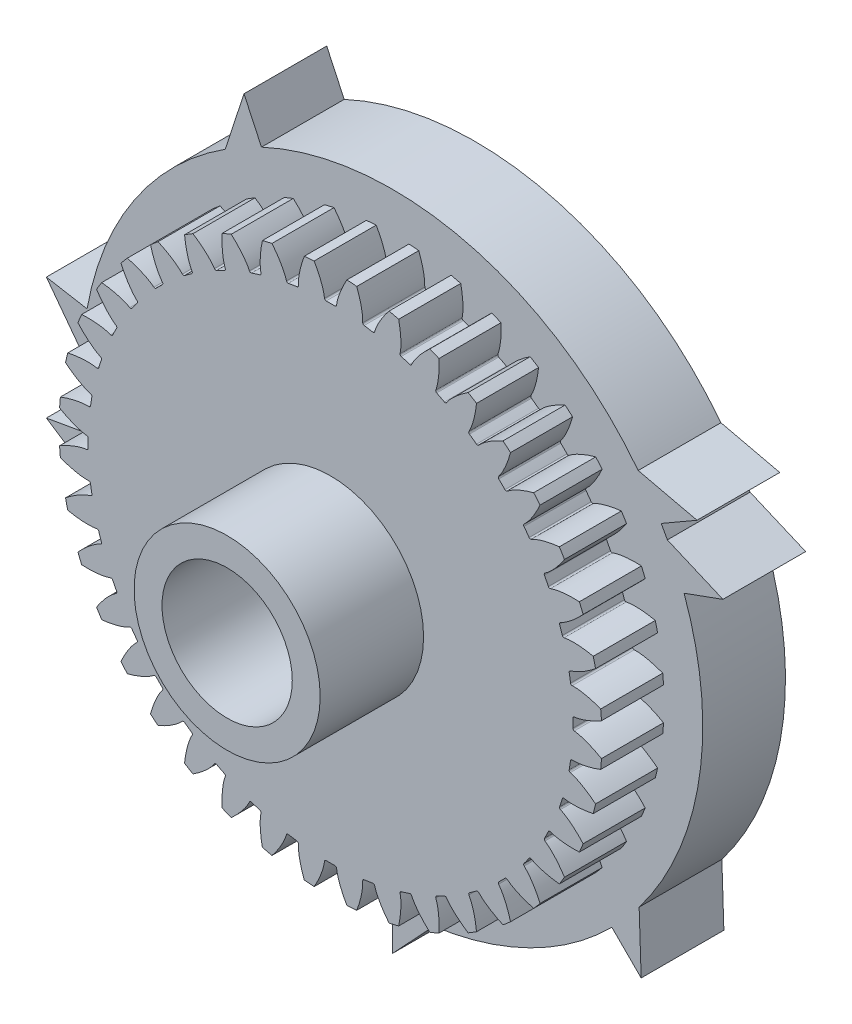
SolidWorks part; units mm, degrees
ref_plane "Front Plane" through (0, 0, 0) normal (0, 0, 1) x (1, 0, 0)
ref_plane "Top Plane" through (0, 0, 0) normal (0, 1, 0) x (1, 0, 0)
ref_plane "Right Plane" through (0, 0, 0) normal (1, 0, 0) x (0, 0, -1)
sketch "D" plane through (0, 0, 0) normal (0, 0, 1) x (1, 0, 0)
  circle A0 centre (0, 0) radius 12.5 construction
  dimension "D1" = 25
sketch "De, Di, Db" plane through (0, 0, 0) normal (0, 0, 1) x (1, 0, 0)
  circle A0 centre (0, 0) radius 11.7462 construction
  circle A1 centre (0, 0) radius 13.125 construction
  circle A2 centre (0, 0) radius 11.7188 construction
  point P7 (0, 0)
  dimension "D1" = 23.4923
  dimension "D2" = 26.25
  dimension "D3" = 23.4375
sketch "Sketch4" plane through (0, 0, 0) normal (0, 0, 1) x (1, 0, 0)
  circle A0 centre (0, 0) radius 13.125 construction
  circle A1 centre (0, 0) radius 13.125
extrude "Addendum Extruded" add sketch "Sketch4" along normal mid plane 3
sketch "Tooth Profile Curve" plane through (0, 0, 0) normal (0, 0, 1) x (1, 0, 0)
  line L0 (0, 0) -> (13.125, 0) construction
  line L1 (0, 0) -> (11.7427, 0.287) construction
  line L2 (0, 0) -> (12.4904, 0.4907) construction
  line L3 (11.7427, 0.287) -> (11.7153, 0.2863)
  line L4 (11.7188, 0) -> (13.125, 0)
  circle A0 centre (0, 0) radius 11.7462 construction
  circle A1 centre (0, 0) radius 13.125 construction
  circle A2 centre (0, 0) radius 11.7188 construction
  circle A3 centre (0, 0) radius 12.5 construction
  arc A4 (11.7153, 0.2863) -> (11.7188, 0) centre (0, 0) cw
  arc A5 (13.125, 0) -> (13.1011, 0.7919) centre (0, 0) ccw
  spline S0 degree 4 poles (11.7427, 0.287) (11.7513, 0.2874) (11.7756, 0.289) (11.8214, 0.2944) (11.8958, 0.3063) (11.9898, 0.3261) (12.1104, 0.3571) (12.2508, 0.4002) (12.4033, 0.4546) (12.567, 0.5213) (12.728, 0.5943) (12.8863, 0.6731) (13.0419, 0.757) (13.2276, 0.8647) (13.4463, 1.0026) (13.6956, 1.1758) (13.9706, 1.3865) (14.2417, 1.6158) (14.5008, 1.8533) (14.7531, 2.1063) (14.9904, 2.3604) (15.2265, 2.6369) (15.4391, 2.8987) (15.6651, 3.2052) (15.844, 3.4566) (16.0663, 3.8016) (16.1935, 4.0093) (16.3375, 4.2568) (16.3989, 4.369) (16.4368, 4.438) knots 0 0 0 0 0 0.005377 0.015084 0.028532 0.04661 0.064855 0.092111 0.119476 0.146842 0.174209 0.201575 0.228941 0.256307 0.307035 0.361767 0.4165 0.471232 0.525964 0.580697 0.635429 0.690161 0.744894 0.799626 0.854358 0.909091 0.954545 1 1 1 1 1 construction
  spline S1 degree 4 poles (11.7427, 0.287) (11.7513, 0.2874) (11.7756, 0.289) (11.8214, 0.2944) (11.8958, 0.3063) (11.9898, 0.3261) (12.1104, 0.3571) (12.2508, 0.4002) (12.4033, 0.4546) (12.567, 0.5213) (12.728, 0.5943) (12.8863, 0.6731) (13.0419, 0.757) (13.2276, 0.8647) (13.4463, 1.0026) (13.6956, 1.1758) (13.9706, 1.3865) (14.2417, 1.6158) (14.5008, 1.8533) (14.7531, 2.1063) (14.9904, 2.3604) (15.2265, 2.6369) (15.4391, 2.8987) (15.6651, 3.2052) (15.844, 3.4566) (16.0181, 3.7268) (16.1013, 3.8598) (16.1431, 3.9284) knots 0 0 0 0 0 0.005377 0.015084 0.028532 0.04661 0.064855 0.092111 0.119476 0.146842 0.174209 0.201575 0.228941 0.256307 0.307035 0.361767 0.4165 0.471232 0.525964 0.580697 0.635429 0.690161 0.744894 0.799626 0.854358 0.909091 0.909091 0.909091 0.909091 0.909091
  dimension "D1" = 2.25
  dimension "D2" = 0.85
  dimension "D3" = 1.4
extrude "1/2 Tooth Cut" cut sketch "Tooth Profile Curve" against normal mid plane 4
ref_plane "Plane of Mirroring" through (0, 0, 0) normal (0, 1, 0) x (1, 0, 0)
mirror "Mirror Tooth Cut" about plane through (0, 0, 0) normal (0, 1, 0) of "1/2 Tooth Cut"
fillet "Roots Fillet" radius 0.0781 3 edges at (11.7427, -0.287, 0) (11.7153, -0.2863, 0) (11.7153, 0.2863, 0)
pattern_circular "Circular Pattern of Teeth" count 40 over 360 about axis through (0, 0, -2) along (0, 0, 1) of "Mirror Tooth Cut", "1/2 Tooth Cut", "Roots Fillet"
sketch "Sketch5" plane through (0, 0, 0) normal (0, 0, 1) x (1, 0, 0)
  line L0 (1, 4) -> (-1, 4) construction
  line L1 (-1, 5) -> (1, 5)
  line L2 (-1, 5) -> (-1, 3.873)
  line L5 (1, 4) -> (1, 5)
  line L6 (1, 4) -> (1, 3.873)
  arc A0 (-1, 3.873) -> (1, 3.873) centre (0, 0) ccw
  circle A1 centre (0, 0) radius 4 construction
  point P9 (0, 5)
  dimension "D1" = 8
  dimension "D2" = 1
  dimension "D3" = 2
extrude "Bore and Keyway" cut sketch "Sketch5" against normal through all both and the other way through all
sketch "Sketch6" [suppressed] plane through (0, 0, 0) normal (0, 0, 1) x (1, 0, 0)
  line L6 (41.8591, 5.9947) -> (34.5048, 4.9415) construction
  line L7 (37.3883, 19.7543) -> (30.8195, 16.2837) construction
  line L8 (41.8591, 5.9947) -> (34.5048, 4.9415)
  line L9 (37.3883, 19.7543) -> (30.8195, 16.2837)
  arc A14 (52.1159, 14.1398) -> (50.4738, 19.1936) centre (0, 0) ccw construction
  arc A20 (34.5048, 4.9415) -> (33.5461, 3.7044) centre (34.6643, 3.8278) ccw construction
  arc A29 (29.3167, 16.721) -> (30.8195, 16.2837) centre (30.294, 17.2784) ccw construction
  circle A30 centre (0, 0) radius 33.75 construction
  arc A31 (52.1159, 14.1398) -> (50.4738, 19.1936) centre (0, 0) ccw
  arc A32 (34.5048, 4.9415) -> (33.5461, 3.7044) centre (34.6643, 3.8278) ccw
  arc A33 (29.3167, 16.721) -> (30.8195, 16.2837) centre (30.294, 17.2784) ccw
  arc A34 (29.3167, 16.721) -> (33.5461, 3.7044) centre (0, 0) ccw
  spline S2 degree 4 poles (965.1968, -1751.9554) (49.5722, -17.509) (34.0199, 17.1415) (35.6787, 19.1473) (37.9033, 19.963) (38.3849, 20.1134) (39.1305, 20.2925) (39.9677, 20.4275) (40.8649, 20.5145) (41.6597, 20.5534) (42.2962, 20.5635) (43.0686, 20.5519) (43.9989, 20.5031) (45.0849, 20.3985) (46.322, 20.2188) (47.5725, 19.978) (64.8653, 15.8708) (78.7396, -0.7897) (70.5074, -3.2513) (1756.2094, -1025.0114) knots -0.360808 -0.360808 -0.360808 -0.360808 -0.360808 0.005377 0.015084 0.028532 0.04661 0.092111 0.146842 0.174209 0.201575 0.228941 0.256307 0.307035 0.361767 0.4165 0.471232 0.525964 3.418372 3.418372 3.418372 3.418372 3.418372 only from (37.3883, 19.7543) to (50.4738, 19.1936) construction
  spline S3 degree 4 poles (-248.913, 1984.6901) (29.8132, 43.3029) (37.5982, 6.1286) (40.1192, 5.4809) (42.3983, 6.1286) (42.8764, 6.29) (43.5848, 6.5834) (44.3415, 6.9662) (45.1185, 7.4233) (45.7844, 7.859) (46.3053, 8.2249) (46.9233, 8.6882) (47.6473, 9.2745) (48.4644, 9.9975) (49.3596, 10.87) (50.2297, 11.7999) (61.8058, 25.2872) (63.2375, 46.9208) (55.1306, 44.0736) (818.3166, 1861.5256) knots -0.360808 -0.360808 -0.360808 -0.360808 -0.360808 0.005377 0.015084 0.028532 0.04661 0.092111 0.146842 0.174209 0.201575 0.228941 0.256307 0.307035 0.361767 0.4165 0.471232 0.525964 3.418372 3.418372 3.418372 3.418372 3.418372 only from (41.8591, 5.9947) to (52.1159, 14.1398) construction
  spline S4 degree 4 poles (37.3883, 19.7543) (37.4162, 19.7684) (37.4955, 19.8059) (37.6488, 19.8697) (37.9033, 19.963) (38.3849, 20.1134) (39.1305, 20.2925) (39.9677, 20.4275) (40.8649, 20.5145) (41.6597, 20.5534) (42.2962, 20.5635) (43.0686, 20.5519) (43.9989, 20.5031) (45.0849, 20.3985) (46.322, 20.2188) (47.5725, 19.978) (48.7682, 19.694) (49.6459, 19.4492) (50.2125, 19.2764) (50.4738, 19.1936) knots 0 0 0 0 0 0.005377 0.015084 0.028532 0.04661 0.092111 0.146842 0.174209 0.201575 0.228941 0.256307 0.307035 0.361767 0.4165 0.471232 0.525964 0.573123 0.573123 0.573123 0.573123 0.573123
  spline S5 degree 4 poles (41.8591, 5.9947) (41.8899, 5.9998) (41.9761, 6.016) (42.1376, 6.0545) (42.3983, 6.1286) (42.8764, 6.29) (43.5848, 6.5834) (44.3415, 6.9662) (45.1185, 7.4233) (45.7844, 7.859) (46.3053, 8.2249) (46.9233, 8.6882) (47.6473, 9.2745) (48.4644, 9.9975) (49.3596, 10.87) (50.2297, 11.7999) (51.0302, 12.7325) (51.5963, 13.4464) (51.9531, 13.9192) (52.1159, 14.1398) knots 0 0 0 0 0 0.005377 0.015084 0.028532 0.04661 0.092111 0.146842 0.174209 0.201575 0.228941 0.256307 0.307035 0.361767 0.4165 0.471232 0.525964 0.573123 0.573123 0.573123 0.573123 0.573123
extrude "Teeth Removing" [suppressed] cut sketch "Sketch6" against normal through all both flip side to cut
sketch "Sketch7" [suppressed] plane through (0, 0, 0) normal (0, 0, 1) x (1, 0, 0)
  line L0 (-3, 10) -> (3, 10)
  line L1 (3, 10) -> (3, 7.4162)
  line L2 (-3, 10) -> (-3, 7.4162)
  arc A0 (-3, 7.4162) -> (3, 7.4162) centre (0, 0) ccw
  point P1 (0, 10)
  dimension "D1" = 8
  dimension "D2" = 10
  dimension "D3" = 6
extrude "Cut-Extrude1" [suppressed] cut sketch "Sketch7" against normal through all both and the other way through all
sketch "Sketch8" [suppressed] plane through (0, 0, 0) normal (0, 0, 1) x (1, 0, 0)
  line L0 (-4.8226, 27.7752) -> (-3.9753, 22.8953) construction
  line L1 (4.8226, 27.7752) -> (3.9753, 22.8953) construction
  line L2 (-4.8226, 27.7752) -> (-3.9753, 22.8953)
  line L3 (4.8226, 27.7752) -> (3.9753, 22.8953)
  arc A0 (-4.5622, 22.0326) -> (4.5622, 22.0326) centre (0, 0) ccw
  arc A1 (-4.5622, 22.0326) -> (-3.9753, 22.8953) centre (-4.7142, 22.767) ccw construction
  arc A2 (3.9753, 22.8953) -> (4.5622, 22.0326) centre (4.7142, 22.767) ccw construction
  arc A3 (-4.5622, 22.0326) -> (-3.9753, 22.8953) centre (-4.7142, 22.767) ccw
  arc A4 (3.9753, 22.8953) -> (4.5622, 22.0326) centre (4.7142, 22.767) ccw
  arc A5 (-1.7713, 35.9564) -> (1.7713, 35.9564) centre (0, 0) cw
  spline S0 degree 4 poles (-2951.1447, 536.0596) (-42.0553, 30.3098) (3.4186, 24.472) (4.7778, 26.2412) (4.8488, 28.1447) (4.8449, 28.481) (4.8049, 28.9907) (4.718, 29.5493) (4.5883, 30.1361) (4.4492, 30.6481) (4.3245, 31.0537) (4.1581, 31.541) (3.9355, 32.1209) (3.6454, 32.7879) (3.2766, 33.5352) (2.8663, 34.2784) (-4.9345, 47.0779) (-24.4948, 52.3174) (-14.1166, 37.6796) (-2283.6828, 1979.2083) knots -0.444693 -0.444693 -0.444693 -0.444693 -0.444693 0.005377 0.015084 0.028532 0.04661 0.092111 0.146842 0.174209 0.201575 0.228941 0.256307 0.307035 0.361767 0.4165 0.471232 0.525964 4.228351 4.228351 4.228351 4.228351 4.228351 only from (4.8226, 27.7752) to (1.7713, 35.9564) construction
  spline S1 degree 4 poles (2951.1447, 536.0596) (42.0553, 30.3098) (-3.4186, 24.472) (-4.7778, 26.2412) (-4.8488, 28.1447) (-4.8449, 28.481) (-4.8049, 28.9907) (-4.718, 29.5493) (-4.5883, 30.1361) (-4.4492, 30.6481) (-4.3245, 31.0537) (-4.1581, 31.541) (-3.9355, 32.1209) (-3.6454, 32.7879) (-3.2766, 33.5352) (-2.8663, 34.2784) (4.9345, 47.0779) (24.4948, 52.3174) (14.1166, 37.6796) (2283.6828, 1979.2083) knots -0.444693 -0.444693 -0.444693 -0.444693 -0.444693 0.005377 0.015084 0.028532 0.04661 0.092111 0.146842 0.174209 0.201575 0.228941 0.256307 0.307035 0.361767 0.4165 0.471232 0.525964 4.228351 4.228351 4.228351 4.228351 4.228351 only from (-4.8226, 27.7752) to (-1.7713, 35.9564) construction
  spline S2 degree 4 poles (4.8226, 27.7752) (4.8257, 27.7958) (4.8332, 27.8538) (4.842, 27.9641) (4.8488, 28.1447) (4.8449, 28.481) (4.8049, 28.9907) (4.718, 29.5493) (4.5883, 30.1361) (4.4492, 30.6481) (4.3245, 31.0537) (4.1581, 31.541) (3.9355, 32.1209) (3.6454, 32.7879) (3.2766, 33.5352) (2.8663, 34.2784) (2.4399, 34.9781) (2.1039, 35.4841) (1.8776, 35.8078) (1.7713, 35.9564) knots 0 0 0 0 0 0.005377 0.015084 0.028532 0.04661 0.092111 0.146842 0.174209 0.201575 0.228941 0.256307 0.307035 0.361767 0.4165 0.471232 0.525964 0.573122 0.573122 0.573122 0.573122 0.573122
  spline S3 degree 4 poles (-4.8226, 27.7752) (-4.8257, 27.7958) (-4.8332, 27.8538) (-4.842, 27.9641) (-4.8488, 28.1447) (-4.8449, 28.481) (-4.8049, 28.9907) (-4.718, 29.5493) (-4.5883, 30.1361) (-4.4492, 30.6481) (-4.3245, 31.0537) (-4.1581, 31.541) (-3.9355, 32.1209) (-3.6454, 32.7879) (-3.2766, 33.5352) (-2.8663, 34.2784) (-2.4399, 34.9781) (-2.1039, 35.4841) (-1.8776, 35.8078) (-1.7713, 35.9564) knots 0 0 0 0 0 0.005377 0.015084 0.028532 0.04661 0.092111 0.146842 0.174209 0.201575 0.228941 0.256307 0.307035 0.361767 0.4165 0.471232 0.525964 0.573122 0.573122 0.573122 0.573122 0.573122
extrude "Cut-Extrude2" [suppressed] cut sketch "Sketch8" against normal through all both and the other way through all flip side to cut
sketch "Sketch9" [suppressed] plane through (0, 0, 0) normal (0, 0, 1) x (1, 0, 0)
  circle A0 centre (0, 0) radius 4
  dimension "D1" = 8
extrude "Cut-Extrude3" [suppressed] cut sketch "Sketch9" against normal through all both and the other way through all
sketch "Sketch10" [suppressed] plane through (0, 0, 0) normal (0, 0, 1) x (1, 0, 0)
  circle A0 centre (0, 0) radius 6
  dimension "D1" = 12
extrude "Cut-Extrude4" [suppressed] cut sketch "Sketch10" against normal through all both and the other way through all
sketch "Sketch11" [suppressed] plane through (0, 0, 0) normal (0, 0, 1) x (1, 0, 0)
  line L0 (27.9061, 3.9965) -> (23.0032, 3.2943) construction
  line L1 (24.9255, 13.1696) -> (20.5463, 10.8558) construction
  line L2 (-4.8226, 27.7752) -> (-3.9753, 22.8953) construction
  line L3 (4.8226, 27.7752) -> (3.9753, 22.8953) construction
  line L4 (27.9061, 3.9965) -> (23.0032, 3.2943)
  line L5 (24.9255, 13.1696) -> (20.5463, 10.8558)
  line L6 (-4.8226, 27.7752) -> (-3.9753, 22.8953)
  line L7 (4.8226, 27.7752) -> (3.9753, 22.8953)
  arc A0 (-4.5622, 22.0326) -> (22.3641, 2.4696) centre (0, 0) ccw
  arc A1 (19.5445, 11.1473) -> (20.5463, 10.8558) centre (20.196, 11.5189) ccw construction
  arc A2 (23.0032, 3.2943) -> (22.3641, 2.4696) centre (23.1095, 2.5519) ccw construction
  arc A4 (3.9753, 22.8953) -> (4.5622, 22.0326) centre (4.7142, 22.767) ccw construction
  arc A5 (19.5445, 11.1473) -> (20.5463, 10.8558) centre (20.196, 11.5189) ccw
  arc A6 (23.0032, 3.2943) -> (22.3641, 2.4696) centre (23.1095, 2.5519) ccw
  arc A7 (-4.5622, 22.0326) -> (-3.9753, 22.8953) centre (-4.7142, 22.767) ccw construction
  arc A8 (3.9753, 22.8953) -> (4.5622, 22.0326) centre (4.7142, 22.767) ccw
  arc A9 (19.5445, 11.1473) -> (4.5622, 22.0326) centre (0, 0) ccw
  arc A10 (-1.7713, 35.9564) -> (1.7713, 35.9564) centre (0, 0) cw
  arc A11 (33.6492, 12.7957) -> (34.7439, 9.4265) centre (0, 0) cw
  arc A12 (-4.5622, 22.0326) -> (-3.9753, 22.8953) centre (-4.7142, 22.767) ccw
  spline S0 degree 4 poles (-402.1308, 2972.3569) (15.8305, 49.3632) (24.3306, 4.311) (26.4333, 3.565) (28.2656, 4.0857) (28.5842, 4.1933) (29.0566, 4.3889) (29.561, 4.6441) (30.079, 4.9488) (30.5229, 5.2393) (30.8702, 5.4833) (31.2822, 5.7922) (31.7649, 6.183) (32.3096, 6.665) (32.9064, 7.2467) (33.4865, 7.8666) (43.2489, 19.2409) (42.1875, 39.4629) (31.4732, 25.0693) (1176.6422, 2783.5204) knots -0.444693 -0.444693 -0.444693 -0.444693 -0.444693 0.005377 0.015084 0.028532 0.04661 0.092111 0.146842 0.174209 0.201575 0.228941 0.256307 0.307035 0.361767 0.4165 0.471232 0.525964 4.228351 4.228351 4.228351 4.228351 4.228351 only from (27.9061, 3.9965) to (34.7439, 9.4265) construction
  spline S1 degree 4 poles (1421.7769, -2641.0538) (41.8221, -30.6307) (22.2178, 10.8135) (23.4804, 12.6529) (25.2689, 13.3086) (25.5899, 13.4089) (26.087, 13.5283) (26.6451, 13.6183) (27.2433, 13.6763) (27.7732, 13.7022) (28.1975, 13.709) (28.7124, 13.7013) (29.3326, 13.6688) (30.0566, 13.599) (30.8813, 13.4792) (31.715, 13.3187) (46.2986, 9.8549) (57.3261, -7.129) (40.1977, -1.782) (2588.0358, -1560.3024) knots -0.444693 -0.444693 -0.444693 -0.444693 -0.444693 0.005377 0.015084 0.028532 0.04661 0.092111 0.146842 0.174209 0.201575 0.228941 0.256307 0.307035 0.361767 0.4165 0.471232 0.525964 4.228351 4.228351 4.228351 4.228351 4.228351 only from (24.9255, 13.1696) to (33.6492, 12.7957) construction
  spline S2 degree 4 poles (2951.1447, 536.0596) (42.0553, 30.3098) (-3.4186, 24.472) (-4.7778, 26.2412) (-4.8488, 28.1447) (-4.8449, 28.481) (-4.8049, 28.9907) (-4.718, 29.5493) (-4.5883, 30.1361) (-4.4492, 30.6481) (-4.3245, 31.0537) (-4.1581, 31.541) (-3.9355, 32.1209) (-3.6454, 32.7879) (-3.2766, 33.5352) (-2.8663, 34.2784) (4.9345, 47.0779) (24.4948, 52.3174) (14.1166, 37.6796) (2283.6828, 1979.2083) knots -0.444693 -0.444693 -0.444693 -0.444693 -0.444693 0.005377 0.015084 0.028532 0.04661 0.092111 0.146842 0.174209 0.201575 0.228941 0.256307 0.307035 0.361767 0.4165 0.471232 0.525964 4.228351 4.228351 4.228351 4.228351 4.228351 only from (-4.8226, 27.7752) to (-1.7713, 35.9564) construction
  spline S3 degree 4 poles (-2951.1447, 536.0596) (-42.0553, 30.3098) (3.4186, 24.472) (4.7778, 26.2412) (4.8488, 28.1447) (4.8449, 28.481) (4.8049, 28.9907) (4.718, 29.5493) (4.5883, 30.1361) (4.4492, 30.6481) (4.3245, 31.0537) (4.1581, 31.541) (3.9355, 32.1209) (3.6454, 32.7879) (3.2766, 33.5352) (2.8663, 34.2784) (-4.9345, 47.0779) (-24.4948, 52.3174) (-14.1166, 37.6796) (-2283.6828, 1979.2083) knots -0.444693 -0.444693 -0.444693 -0.444693 -0.444693 0.005377 0.015084 0.028532 0.04661 0.092111 0.146842 0.174209 0.201575 0.228941 0.256307 0.307035 0.361767 0.4165 0.471232 0.525964 4.228351 4.228351 4.228351 4.228351 4.228351 only from (4.8226, 27.7752) to (1.7713, 35.9564) construction
  spline S4 degree 4 poles (27.9061, 3.9965) (27.9266, 3.9998) (27.9841, 4.0106) (28.0917, 4.0363) (28.2656, 4.0857) (28.5842, 4.1933) (29.0566, 4.3889) (29.561, 4.6441) (30.079, 4.9488) (30.5229, 5.2393) (30.8702, 5.4833) (31.2822, 5.7922) (31.7649, 6.183) (32.3096, 6.665) (32.9064, 7.2467) (33.4865, 7.8666) (34.0201, 8.4883) (34.3975, 8.9643) (34.6354, 9.2795) (34.7439, 9.4265) knots 0 0 0 0 0 0.005377 0.015084 0.028532 0.04661 0.092111 0.146842 0.174209 0.201575 0.228941 0.256307 0.307035 0.361767 0.4165 0.471232 0.525964 0.573122 0.573122 0.573122 0.573122 0.573122
  spline S5 degree 4 poles (24.9255, 13.1696) (24.9442, 13.1789) (24.997, 13.204) (25.0992, 13.2464) (25.2689, 13.3086) (25.5899, 13.4089) (26.087, 13.5283) (26.6451, 13.6183) (27.2433, 13.6763) (27.7732, 13.7022) (28.1975, 13.709) (28.7124, 13.7013) (29.3326, 13.6688) (30.0566, 13.599) (30.8813, 13.4792) (31.715, 13.3187) (32.5122, 13.1293) (33.0972, 12.9661) (33.475, 12.8509) (33.6492, 12.7957) knots 0 0 0 0 0 0.005377 0.015084 0.028532 0.04661 0.092111 0.146842 0.174209 0.201575 0.228941 0.256307 0.307035 0.361767 0.4165 0.471232 0.525964 0.573122 0.573122 0.573122 0.573122 0.573122
  spline S6 degree 4 poles (-4.8226, 27.7752) (-4.8257, 27.7958) (-4.8332, 27.8538) (-4.842, 27.9641) (-4.8488, 28.1447) (-4.8449, 28.481) (-4.8049, 28.9907) (-4.718, 29.5493) (-4.5883, 30.1361) (-4.4492, 30.6481) (-4.3245, 31.0537) (-4.1581, 31.541) (-3.9355, 32.1209) (-3.6454, 32.7879) (-3.2766, 33.5352) (-2.8663, 34.2784) (-2.4399, 34.9781) (-2.1039, 35.4841) (-1.8776, 35.8078) (-1.7713, 35.9564) knots 0 0 0 0 0 0.005377 0.015084 0.028532 0.04661 0.092111 0.146842 0.174209 0.201575 0.228941 0.256307 0.307035 0.361767 0.4165 0.471232 0.525964 0.573122 0.573122 0.573122 0.573122 0.573122
  spline S7 degree 4 poles (4.8226, 27.7752) (4.8257, 27.7958) (4.8332, 27.8538) (4.842, 27.9641) (4.8488, 28.1447) (4.8449, 28.481) (4.8049, 28.9907) (4.718, 29.5493) (4.5883, 30.1361) (4.4492, 30.6481) (4.3245, 31.0537) (4.1581, 31.541) (3.9355, 32.1209) (3.6454, 32.7879) (3.2766, 33.5352) (2.8663, 34.2784) (2.4399, 34.9781) (2.1039, 35.4841) (1.8776, 35.8078) (1.7713, 35.9564) knots 0 0 0 0 0 0.005377 0.015084 0.028532 0.04661 0.092111 0.146842 0.174209 0.201575 0.228941 0.256307 0.307035 0.361767 0.4165 0.471232 0.525964 0.573122 0.573122 0.573122 0.573122 0.573122
extrude "Cut-Extrude6" [suppressed] cut sketch "Sketch11" against normal through all both and the other way through all flip side to cut
sketch "Sketch12" [suppressed] plane through (0, 0, 0) normal (0, 0, 1) x (1, 0, 0)
  line L0 (-20.2274, -19.636) -> (-16.6736, -16.1861) construction
  line L1 (-12.4243, -25.3053) -> (-10.2415, -20.8593) construction
  line L2 (4.8226, 27.7752) -> (3.9753, 22.8953) construction
  line L3 (-4.8226, 27.7752) -> (-3.9753, 22.8953) construction
  line L4 (-20.2274, -19.636) -> (-16.6736, -16.1861)
  line L5 (-12.4243, -25.3053) -> (-10.2415, -20.8593)
  line L6 (4.8226, 27.7752) -> (3.9753, 22.8953)
  line L7 (-4.8226, 27.7752) -> (-3.9753, 22.8953)
  arc A0 (-9.2596, -20.5063) -> (4.5622, 22.0326) centre (0, 0) ccw
  arc A1 (-9.2596, -20.5063) -> (-10.2415, -20.8593) centre (-9.5682, -21.1899) ccw construction
  arc A2 (-16.6736, -16.1861) -> (-16.6413, -15.1432) centre (-17.196, -15.648) ccw construction
  arc A3 (-4.5622, 22.0326) -> (-3.9753, 22.8953) centre (-4.7142, 22.767) ccw construction
  arc A4 (3.9753, 22.8953) -> (4.5622, 22.0326) centre (4.7142, 22.767) ccw construction
  arc A5 (-9.2596, -20.5063) -> (-10.2415, -20.8593) centre (-9.5682, -21.1899) ccw
  arc A6 (-16.6736, -16.1861) -> (-16.6413, -15.1432) centre (-17.196, -15.648) ccw
  arc A7 (-4.5622, 22.0326) -> (-3.9753, 22.8953) centre (-4.7142, 22.767) ccw
  arc A8 (3.9753, 22.8953) -> (4.5622, 22.0326) centre (4.7142, 22.767) ccw
  arc A9 (-4.5622, 22.0326) -> (-16.6413, -15.1432) centre (0, 0) ccw
  arc A10 (1.7713, 35.9564) -> (-1.7713, 35.9564) centre (0, 0) ccw
  arc A11 (-19.7016, -30.1305) -> (-22.5676, -28.0482) centre (0, 0) cw
  spline S0 degree 4 poles (2072.4383, -2168.3207) (16.2078, -49.2406) (-17.15, -17.7889) (-19.2895, -18.4213) (-20.4658, -19.9195) (-20.6604, -20.1939) (-20.9275, -20.6297) (-21.1856, -21.1327) (-21.4256, -21.6837) (-21.614, -22.1796) (-21.7515, -22.5811) (-21.9033, -23.0732) (-22.064, -23.6731) (-22.2214, -24.3832) (-22.3623, -25.2046) (-22.4673, -26.0471) (-23.6796, -40.9873) (-10.9347, -56.7234) (-10.727, -38.7809) (684.1887, -2943.5283) knots -0.444693 -0.444693 -0.444693 -0.444693 -0.444693 0.005377 0.015084 0.028532 0.04661 0.092111 0.146842 0.174209 0.201575 0.228941 0.256307 0.307035 0.361767 0.4165 0.471232 0.525964 4.228351 4.228351 4.228351 4.228351 4.228351 only from (-20.2274, -19.636) to (-22.5676, -28.0482) construction
  spline S1 degree 4 poles (-2702.6142, 1300.958) (-51.8391, 0.1983) (-11.6186, -21.8076) (-11.5589, -24.0379) (-12.6203, -25.6196) (-12.8211, -25.8894) (-13.1531, -26.2782) (-13.5517, -26.6791) (-14.0016, -27.0776) (-14.415, -27.41) (-14.7543, -27.6649) (-15.1754, -27.9613) (-15.6963, -28.2995) (-16.323, -28.6687) (-17.0606, -29.0565) (-17.8295, -29.4166) (-31.6638, -35.1864) (-50.5681, -27.928) (-33.5681, -22.1859) (-3010.8877, -258.8981) knots -0.444693 -0.444693 -0.444693 -0.444693 -0.444693 0.005377 0.015084 0.028532 0.04661 0.092111 0.146842 0.174209 0.201575 0.228941 0.256307 0.307035 0.361767 0.4165 0.471232 0.525964 4.228351 4.228351 4.228351 4.228351 4.228351 only from (-12.4243, -25.3053) to (-19.7016, -30.1305) construction
  spline S2 degree 4 poles (2951.1447, 536.0596) (42.0553, 30.3098) (-3.4186, 24.472) (-4.7778, 26.2412) (-4.8488, 28.1447) (-4.8449, 28.481) (-4.8049, 28.9907) (-4.718, 29.5493) (-4.5883, 30.1361) (-4.4492, 30.6481) (-4.3245, 31.0537) (-4.1581, 31.541) (-3.9355, 32.1209) (-3.6454, 32.7879) (-3.2766, 33.5352) (-2.8663, 34.2784) (4.9345, 47.0779) (24.4948, 52.3174) (14.1166, 37.6796) (2283.6828, 1979.2083) knots -0.444693 -0.444693 -0.444693 -0.444693 -0.444693 0.005377 0.015084 0.028532 0.04661 0.092111 0.146842 0.174209 0.201575 0.228941 0.256307 0.307035 0.361767 0.4165 0.471232 0.525964 4.228351 4.228351 4.228351 4.228351 4.228351 only from (-4.8226, 27.7752) to (-1.7713, 35.9564) construction
  spline S3 degree 4 poles (-2951.1447, 536.0596) (-42.0553, 30.3098) (3.4186, 24.472) (4.7778, 26.2412) (4.8488, 28.1447) (4.8449, 28.481) (4.8049, 28.9907) (4.718, 29.5493) (4.5883, 30.1361) (4.4492, 30.6481) (4.3245, 31.0537) (4.1581, 31.541) (3.9355, 32.1209) (3.6454, 32.7879) (3.2766, 33.5352) (2.8663, 34.2784) (-4.9345, 47.0779) (-24.4948, 52.3174) (-14.1166, 37.6796) (-2283.6828, 1979.2083) knots -0.444693 -0.444693 -0.444693 -0.444693 -0.444693 0.005377 0.015084 0.028532 0.04661 0.092111 0.146842 0.174209 0.201575 0.228941 0.256307 0.307035 0.361767 0.4165 0.471232 0.525964 4.228351 4.228351 4.228351 4.228351 4.228351 only from (4.8226, 27.7752) to (1.7713, 35.9564) construction
  spline S4 degree 4 poles (-20.2274, -19.636) (-20.2421, -19.6508) (-20.2822, -19.6933) (-20.3542, -19.7774) (-20.4658, -19.9195) (-20.6604, -20.1939) (-20.9275, -20.6297) (-21.1856, -21.1327) (-21.4256, -21.6837) (-21.614, -22.1796) (-21.7515, -22.5811) (-21.9033, -23.0732) (-22.064, -23.6731) (-22.2214, -24.3832) (-22.3623, -25.2046) (-22.4673, -26.0471) (-22.5335, -26.8637) (-22.5591, -27.4706) (-22.5663, -27.8654) (-22.5676, -28.0482) knots 0 0 0 0 0 0.005377 0.015084 0.028532 0.04661 0.092111 0.146842 0.174209 0.201575 0.228941 0.256307 0.307035 0.361767 0.4165 0.471232 0.525964 0.573122 0.573122 0.573122 0.573122 0.573122
  spline S5 degree 4 poles (-12.4243, -25.3053) (-12.4339, -25.3238) (-12.4619, -25.3751) (-12.5196, -25.4695) (-12.6203, -25.6196) (-12.8211, -25.8894) (-13.1531, -26.2782) (-13.5517, -26.6791) (-14.0016, -27.0776) (-14.415, -27.41) (-14.7543, -27.6649) (-15.1754, -27.9613) (-15.6963, -28.2995) (-16.323, -28.6687) (-17.0606, -29.0565) (-17.8295, -29.4166) (-18.5857, -29.732) (-19.1549, -29.9439) (-19.5282, -30.0727) (-19.7016, -30.1305) knots 0 0 0 0 0 0.005377 0.015084 0.028532 0.04661 0.092111 0.146842 0.174209 0.201575 0.228941 0.256307 0.307035 0.361767 0.4165 0.471232 0.525964 0.573122 0.573122 0.573122 0.573122 0.573122
  spline S6 degree 4 poles (-4.8226, 27.7752) (-4.8257, 27.7958) (-4.8332, 27.8538) (-4.842, 27.9641) (-4.8488, 28.1447) (-4.8449, 28.481) (-4.8049, 28.9907) (-4.718, 29.5493) (-4.5883, 30.1361) (-4.4492, 30.6481) (-4.3245, 31.0537) (-4.1581, 31.541) (-3.9355, 32.1209) (-3.6454, 32.7879) (-3.2766, 33.5352) (-2.8663, 34.2784) (-2.4399, 34.9781) (-2.1039, 35.4841) (-1.8776, 35.8078) (-1.7713, 35.9564) knots 0 0 0 0 0 0.005377 0.015084 0.028532 0.04661 0.092111 0.146842 0.174209 0.201575 0.228941 0.256307 0.307035 0.361767 0.4165 0.471232 0.525964 0.573122 0.573122 0.573122 0.573122 0.573122
  spline S7 degree 4 poles (4.8226, 27.7752) (4.8257, 27.7958) (4.8332, 27.8538) (4.842, 27.9641) (4.8488, 28.1447) (4.8449, 28.481) (4.8049, 28.9907) (4.718, 29.5493) (4.5883, 30.1361) (4.4492, 30.6481) (4.3245, 31.0537) (4.1581, 31.541) (3.9355, 32.1209) (3.6454, 32.7879) (3.2766, 33.5352) (2.8663, 34.2784) (2.4399, 34.9781) (2.1039, 35.4841) (1.8776, 35.8078) (1.7713, 35.9564) knots 0 0 0 0 0 0.005377 0.015084 0.028532 0.04661 0.092111 0.146842 0.174209 0.201575 0.228941 0.256307 0.307035 0.361767 0.4165 0.471232 0.525964 0.573122 0.573122 0.573122 0.573122 0.573122
extrude "Cut-Extrude7" [suppressed] cut sketch "Sketch12" against normal through all both and the other way through all flip side to cut
sketch "Sketch13" plane through (0, 0, 1.5) normal (0, 0, 1) x (1, 0, 0)
  line L0 (-1, 5) -> (1, 5)
  line L1 (1, 5) -> (1, 3.873)
  line L3 (-1, 3.873) -> (-1, 5)
  arc A0 (-1, 3.873) -> (1, 3.873) centre (0, 0) ccw
extrude "Boss-Extrude1" add sketch "Sketch13" against normal up to surface (3 mm away) up to face at (0, 2.4682, -1.5)
sketch "Sketch14" plane through (0, 0, 1.5) normal (0, 0, 1) x (1, 0, 0)
  circle A0 centre (0, 0) radius 3.15
extrude "Cut-Extrude8" cut sketch "Sketch14" against normal up to next
sketch "Sketch15" plane through (0, 0, 0) normal (0, 0, 1) x (1, 0, 0)
  circle A0 centre (0, 0) radius 3.15
  circle A1 centre (0, 0) radius 4.5
  dimension "D1" = 6.3
  dimension "D2" = 9
extrude "Boss-Extrude2" add sketch "Sketch15" along normal mid plane 13
sketch "Sketch16" plane through (0, 0, -1.5) normal (0, 0, -1) x (-1, 0, 0)
  circle A0 centre (0, 0) radius 15
  circle A1 centre (0, 0) radius 3.15
  dimension "D1" = 30
  dimension "D2" = 6.3
extrude "Boss-Extrude3" add sketch "Sketch16" along normal blind 4
sketch "Sketch17" plane through (0, 0, -5.5) normal (0, 0, -1) x (-1, 0, 0)
  circle A0 centre (0, 0) radius 13.5
  circle A1 centre (0, 0) radius 4.5
  dimension "D1" = 27
  dimension "D2" = 9
extrude "Cut-Extrude9" cut sketch "Sketch17" against normal offset from surface (2 mm away) 2 up to face at (-15, 0, -1.5)
sketch "Sketch18" plane through (0, 0, -3.5) normal (0, 0, -1) x (-1, 0, 0)
  circle A1 centre (0, 0) radius 4.5
  circle A3 centre (0, 0) radius 9.75
  dimension "D2" = 19.5
  dimension "D1" = 9
extrude "Cut-Extrude12" cut sketch "Sketch18" against normal offset from surface (3 mm away) 2
sketch "Sketch20" plane through (0, 0, -5.5) normal (0, 0, -1) x (-1, 0, 0)
  line L0 (-15, -0.5) -> (-3.1101, -0.5)
  line L1 (15, -0.5) -> (15, 0.5)
  line L2 (15, 0.5) -> (3.1101, 0.5)
  line L3 (-15, 0.5) -> (-15, -0.5)
  line L4 (-0.5, 15) -> (-0.5, 3.1101)
  line L5 (-0.5, -15) -> (0.5, -15)
  line L6 (0.5, -15) -> (0.5, -3.1101)
  line L7 (0.5, 15) -> (-0.5, 15)
  line L8 (-30.1424, 0) -> (30.1424, 0) construction
  line L9 (0, 28.1377) -> (0, -19.0188) construction
  line L10 (-3.1101, 0.5) -> (-15, 0.5)
  line L12 (-0.5, -3.1101) -> (-0.5, -15)
  line L13 (0.5, 3.1101) -> (0.5, 15)
  line L14 (3.1101, -0.5) -> (15, -0.5)
  circle A2 centre (0, 0) radius 15 construction
  circle A3 centre (0, 0) radius 3.15
  point P10 (15, 0)
  point P16 (0, 15)
  circle M20 centre (0, 0) radius 13.5
  dimension "D3" = 6.3
  dimension "D1" = 1
  dimension "D2" = 1
  dimension "D4" = 1
extrude "Boss-Extrude5" add sketch "Sketch20" against normal up to body contours A3 L10 L0 M20 | A3 L13 L4 M20 | A3 L14 L2 M20 | A3 L12 L6 M20
sketch "Sketch22" plane through (0, 0, -1.5) normal (0, 0, 1) x (1, 0, 0)
  line L0 (0, 0) -> (0, -33.2695) construction
  line L1 (0, -15) -> (0, -17)
  line L2 (0, -17) -> (1.9956, -14.8667)
  line L3 (-16.7417, 2.952) -> (-14.9873, 0.6163)
  line L4 (-14.7721, 2.6047) -> (-16.7417, 2.952)
  line L5 (-14.7721, -2.6047) -> (-16.7417, -2.952)
  line L6 (-16.7417, -2.952) -> (-14.2943, -4.5468)
  line L7 (10.6066, -10.6066) -> (12.0208, -12.0208)
  line L8 (12.0208, -12.0208) -> (11.9234, -9.1013)
  line L9 (14.0954, 5.1303) -> (15.9748, 5.8143)
  line L10 (15.9748, 5.8143) -> (13.2876, 6.9599)
  line L11 (12.9904, 7.5) -> (14.7224, 8.5)
  line L12 (14.7224, 8.5) -> (11.8771, 9.1615)
  line L13 (-6.3393, 13.5946) -> (-7.1845, 15.4072)
  line L14 (-7.1845, 15.4072) -> (-8.0915, 12.6304)
  circle A0 centre (0, 0) radius 15 construction
  arc A1 (0, -15) -> (1.9956, -14.8667) centre (0, 0) ccw
  arc A2 (-14.7721, -2.6047) -> (-14.2943, -4.5468) centre (0, 0) ccw
  arc A3 (-14.7721, 2.6047) -> (-14.9873, 0.6163) centre (0, 0) ccw
  arc A4 (-6.3393, 13.5946) -> (-8.0915, 12.6304) centre (0, 0) ccw
  arc A5 (12.9904, 7.5) -> (11.8771, 9.1615) centre (0, 0) ccw
  arc A6 (14.0954, 5.1303) -> (13.2876, 6.9599) centre (0, 0) ccw
  arc A7 (10.6066, -10.6066) -> (11.9234, -9.1013) centre (0, 0) ccw
  point P12 (0, 0)
  point P17 (0, 0)
  point P20 (0, 0)
  point P25 (0, 0)
  point P28 (0, 0)
  point P33 (0, 0)
  dimension "D1" = 2
  dimension "D2" = 2
  dimension "D5" = 80
  dimension "D7" = 45
  dimension "D8" = 100
  dimension "D10" = 110
  dimension "D12" = 120
  dimension "D14" = 155
  dimension "D3" = 2
  dimension "D4" = 2
  dimension "D6" = 2
  dimension "D9" = 2
  dimension "D11" = 2
  dimension "D13" = 2
extrude "Boss-Extrude7" add sketch "Sketch22" against normal up to surface (4 mm away)
equation "\"D\"= \"D1@D\"'Pitch Diameter"
equation "\"m\"= 25 / 40'Module"
equation "\"z\"= \"D\" / \"m\"'Numer of Teeth"
equation "\"De\"= \"m\" * ( \"z\" + 2 )'Addendeum Diameter"
equation "\"Di\"= \"m\" * ( \"z\" - 2.5 )'Dedendum Diameter"
equation "\"Phi\"= 20'Pressure Angle"
equation "\"Db\"= \"D\" * cos ( \"Phi\" )'Base Diameter"
equation "\"k\"= \"m\"'Factor k"
equation "\"f\"= 1.25 * \"m\"'Factor f"
equation "\"Rf\"= ( \"f\" - \"k\" ) / 2'Roots Fillet"
equation "\"D1@De, Di, Db\"=\"Db\""
equation "\"D2@De, Di, Db\"=\"De\""
equation "\"D3@De, Di, Db\"=\"Di\""
equation "\"D1@Circular Pattern of Teeth\"=\"z\""
equation "\"D1@Roots Fillet\"=\"Rf\""
equation "\"Teta1\"= 360 / ( 4 * \"z\" )'Angle 1 For Tooth Cut"
equation "\"D1@Tooth Profile Curve\"=\"Teta1\""
equation "\"D3@Tooth Profile Curve\"=\"Teta1\"-\"D2@Tooth Profile Curve\""
equation "\"D1\" = \"Rf\""
